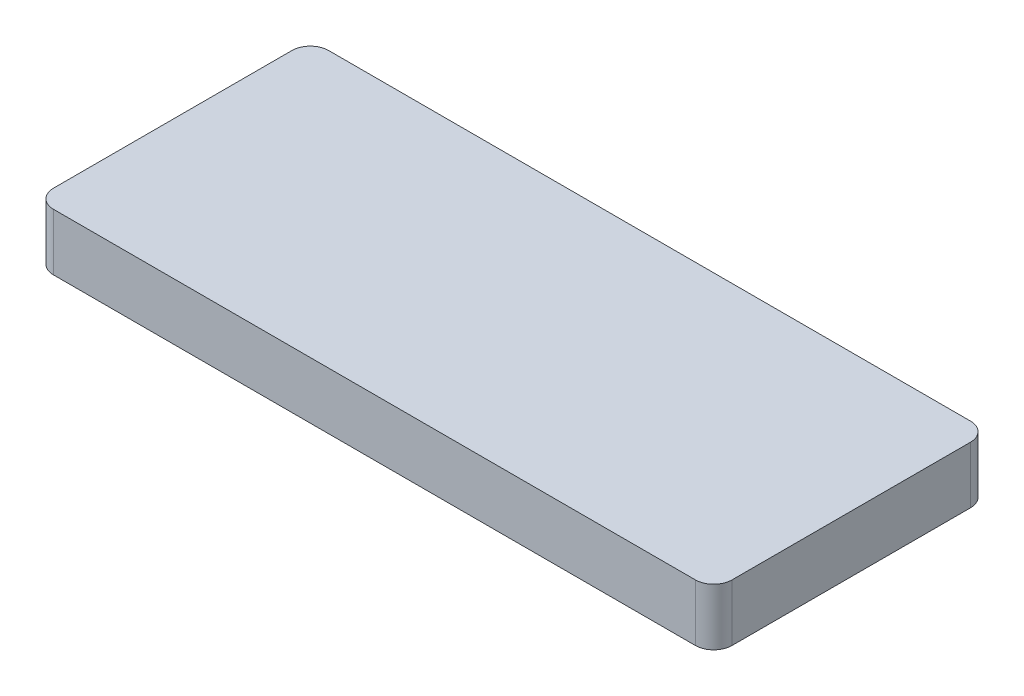
SolidWorks part; units mm, degrees
material "Rubber"
ref_plane "Front Plane" through (0, 0, 0) normal (0, 0, 1) x (1, 0, 0)
ref_plane "Top Plane" through (0, 0, 0) normal (0, 1, 0) x (1, 0, 0)
ref_plane "Right Plane" through (0, 0, 0) normal (1, 0, 0) x (0, 0, -1)
sketch "Sketch1" plane through (0, 0, 0) normal (0, 1, 0) x (1, 0, 0)
  line L1 (-17.5, -7.5) -> (17.5, -7.5)
  line L2 (-18.5, -6.5) -> (-18.5, 6.5)
  line L3 (-17.5, 7.5) -> (17.5, 7.5)
  line L4 (18.5, -6.5) -> (18.5, 6.5)
  line L5 (-18.5, -7.5) -> (18.5, 7.5) construction
  line L6 (-18.5, 7.5) -> (18.5, -7.5) construction
  arc A0 (17.5, -7.5) -> (18.5, -6.5) centre (17.5, -6.5) ccw
  arc A1 (-17.5, -7.5) -> (-18.5, -6.5) centre (-17.5, -6.5) cw
  arc A2 (17.5, 7.5) -> (18.5, 6.5) centre (17.5, 6.5) cw
  arc A3 (-18.5, 6.5) -> (-17.5, 7.5) centre (-17.5, 6.5) cw
  point P0 (0, 0)
  dimension "D3" = 1
  dimension "D1" = 37
  dimension "D2" = 15
extrude "Boss-Extrude1" add sketch "Sketch1" along normal blind 3.1
